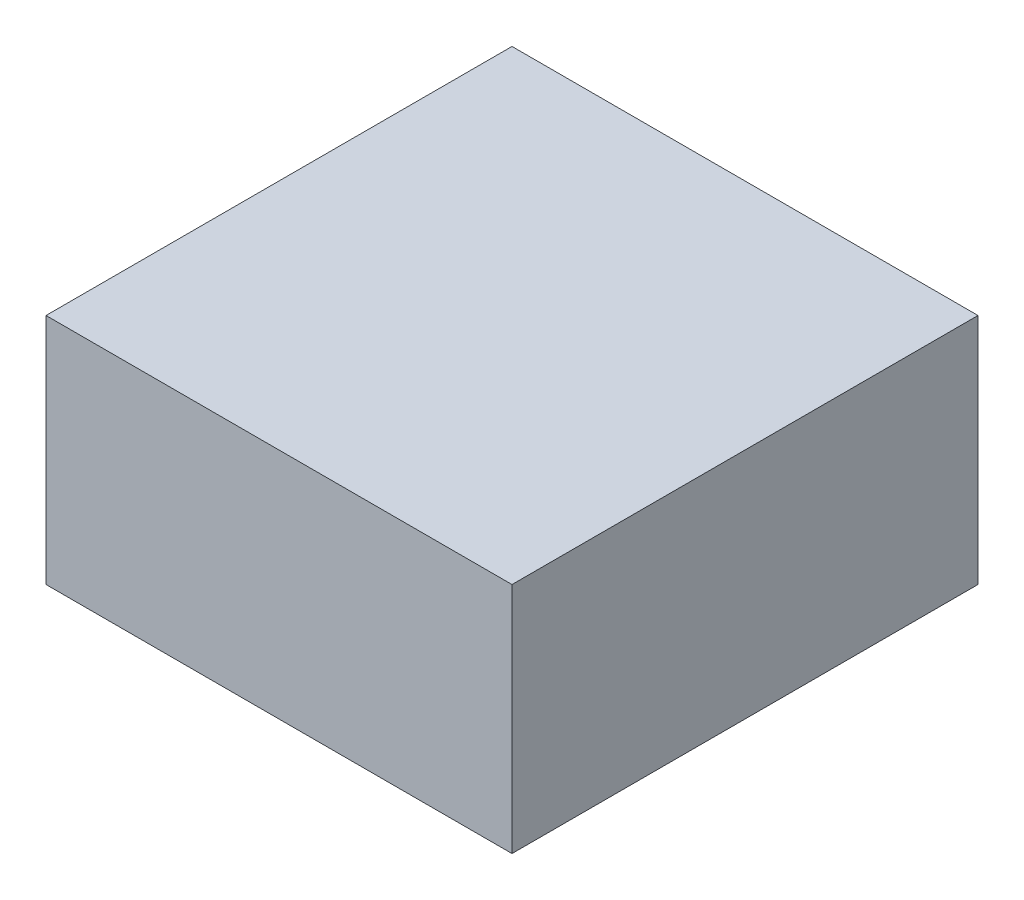
SolidWorks part; units mm, degrees
ref_plane "前视基准面" through (0, 0, 0) normal (0, 0, 1) x (1, 0, 0)
ref_plane "上视基准面" through (0, 0, 0) normal (0, 1, 0) x (1, 0, 0)
ref_plane "右视基准面" through (0, 0, 0) normal (1, 0, 0) x (0, 0, -1)
sketch "草图1" plane through (0, 0, 0) normal (0, 1, 0) x (1, 0, 0)
  line L7 (-25, -25) -> (25, -25)
  line L8 (-25, -25) -> (-25, 25)
  line L9 (-25, 25) -> (25, 25)
  line L10 (25, -25) -> (25, 25)
  line L11 (-25, -25) -> (25, 25) construction
  line L12 (-25, 25) -> (25, -25) construction
  dimension "D1" = 50
  dimension "D3" = 50
extrude "凸台-拉伸1" add sketch "草图1" along normal blind 25
